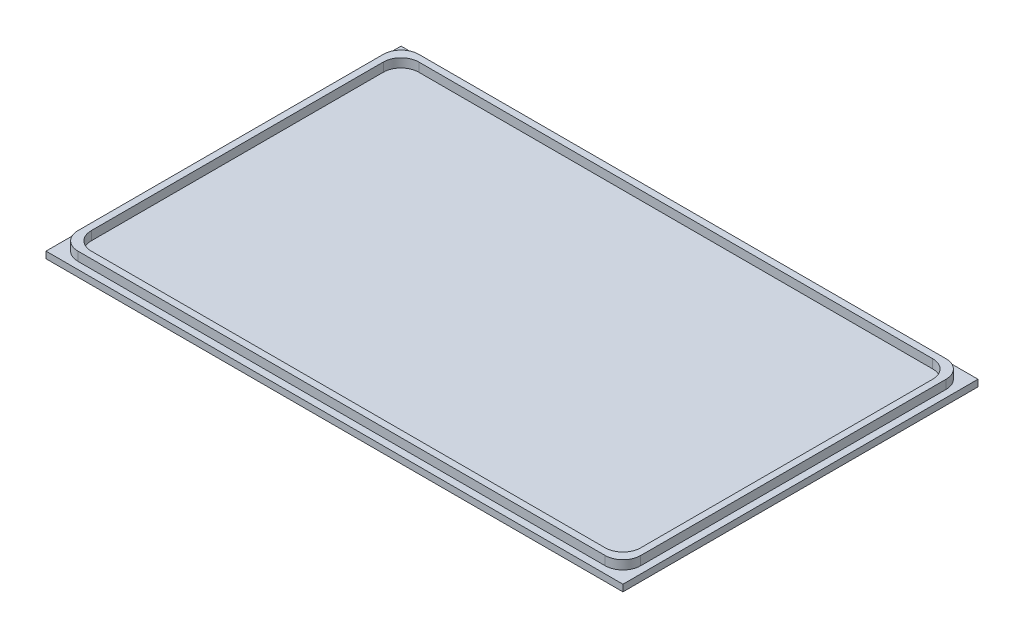
SolidWorks part; units mm, degrees
ref_plane "Ebene vorne" through (0, 0, 0) normal (0, 0, 1) x (1, 0, 0)
ref_plane "Ebene oben" through (0, 0, 0) normal (0, 1, 0) x (1, 0, 0)
ref_plane "Ebene rechts" through (0, 0, 0) normal (1, 0, 0) x (0, 0, -1)
sketch "Sketch1" plane through (0, 0, 0) normal (0, 1, 0) x (1, 0, 0)
  line L1 (-130, -80) -> (130, -80)
  line L2 (-130, -80) -> (-130, 80)
  line L3 (-130, 80) -> (130, 80)
  line L4 (130, -80) -> (130, 80)
  line L5 (-130, -80) -> (130, 80) construction
  line L6 (-130, 80) -> (130, -80) construction
  point P0 (0, 0)
  dimension "D1" = 260
  dimension "D2" = 160
extrude "Boss-Extrude1" add sketch "Sketch1" along normal blind 3
sketch "Sketch2" plane through (0, 3, 0) normal (0, 1, 0) x (1, 0, 0)
  line L0 (126.8, -76.8) -> (126.8, 76.8)
  line L1 (126.8, 76.8) -> (-126.8, 76.8)
  line L2 (-126.8, 76.8) -> (-126.8, -76.8)
  line L3 (-126.8, -76.8) -> (126.8, -76.8)
  line L4 (130, -80) -> (130, 80)
  line L5 (130, 80) -> (-130, 80)
  line L6 (-130, 80) -> (-130, -80)
  line L7 (-130, -80) -> (130, -80)
  line L8 (130, -80) -> (130, 80) construction
  line L9 (130, 80) -> (-130, 80) construction
  line L10 (-130, 80) -> (-130, -80) construction
  line L11 (-130, -80) -> (130, -80) construction
  line L12 (123.8, -73.8) -> (123.8, 73.8)
  line L13 (123.8, 73.8) -> (-123.8, 73.8)
  line L14 (-123.8, 73.8) -> (-123.8, -73.8)
  line L15 (-123.8, -73.8) -> (123.8, -73.8)
  dimension "D1" = 0
  dimension "D2" = 3.2
  dimension "D3" = 3
extrude "Boss-Extrude2" add sketch "Sketch2" along normal blind 4
fillet "Fillet1" radius 8 8 edges at (126.8, 5, -76.8) (123.8, 5, -73.8) (123.8, 5, 73.8) (126.8, 5, 76.8) (-126.8, 5, 76.8) (-123.8, 5, 73.8) (-126.8, 5, -76.8) (-123.8, 5, -73.8)
